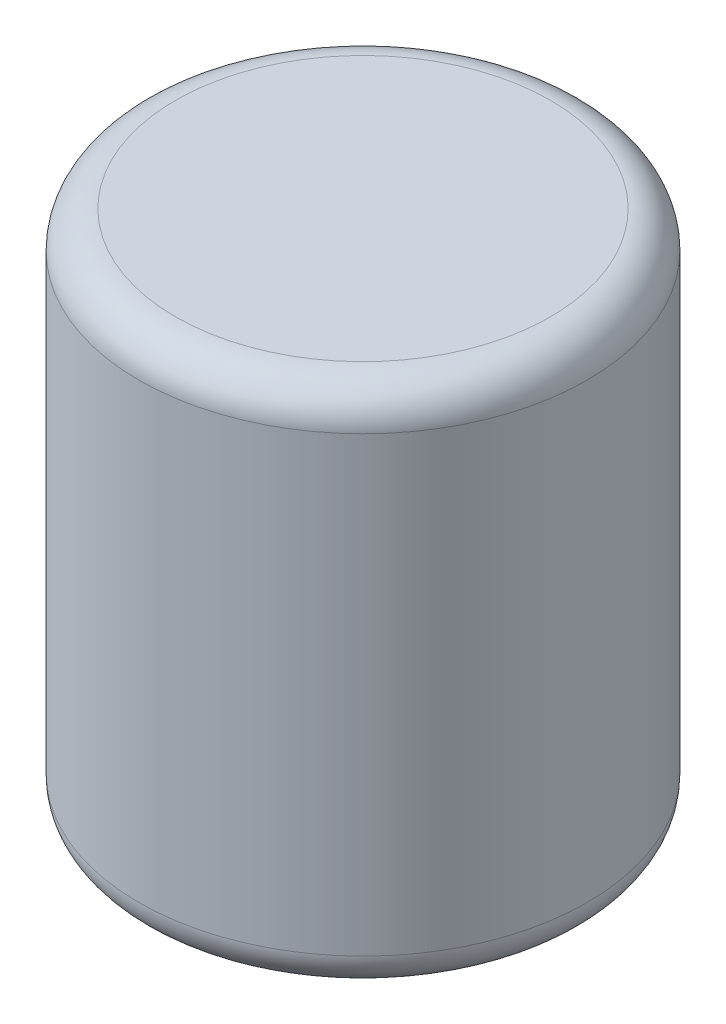
SolidWorks part; units mm, degrees
ref_plane "Front Plane" through (0, 0, 0) normal (0, 0, 1) x (1, 0, 0)
ref_plane "Top Plane" through (0, 0, 0) normal (0, 1, 0) x (1, 0, 0)
ref_plane "Right Plane" through (0, 0, 0) normal (1, 0, 0) x (0, 0, -1)
sketch "Sketch1" plane through (0, 0, 0) normal (0, 1, 0) x (1, 0, 0)
  circle A0 centre (0, 0) radius 31.115
  dimension "D1" = 62.23
extrude "Boss-Extrude1" add sketch "Sketch1" along normal blind 72.9742
fillet "Fillet1" radius 5.08 2 edges at (0, 0, 31.115) (0, 72.9742, 31.115)
